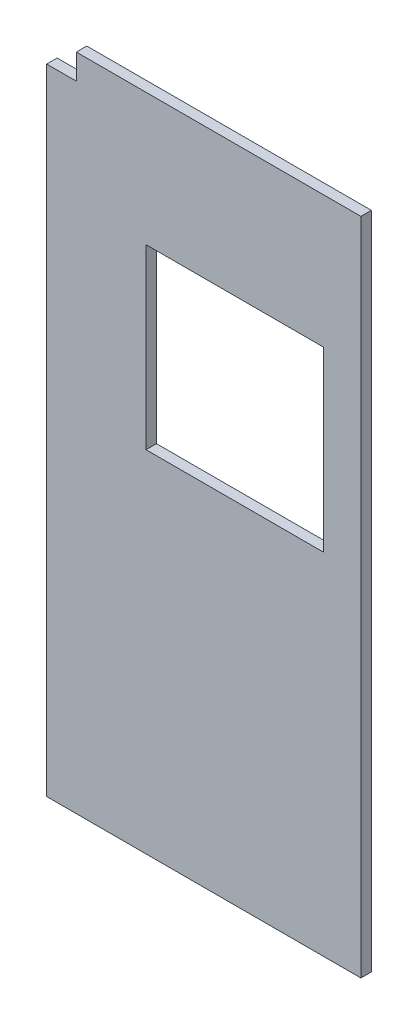
SolidWorks part; units mm, degrees
material "Polyurethane Foam Flexible"
ref_plane "Front Plane" through (0, 0, 0) normal (0, 0, 1) x (1, 0, 0)
ref_plane "Top Plane" through (0, 0, 0) normal (0, 1, 0) x (1, 0, 0)
ref_plane "Right Plane" through (0, 0, 0) normal (1, 0, 0) x (0, 0, -1)
sketch "Sketch1" plane through (0, 0, 0) normal (0, 0, 1) x (1, 0, 0)
  line L1 (-573.151, 1202.944) -> (573.151, 1202.944)
  line L2 (-573.151, 1202.944) -> (-573.151, -1202.944)
  line L3 (-573.151, -1202.944) -> (573.151, -1202.944)
  line L4 (573.151, 1202.944) -> (573.151, -1202.944)
  line L5 (-573.151, 1202.944) -> (573.151, -1202.944) construction
  line L6 (-573.151, -1202.944) -> (573.151, 1202.944) construction
  line L7 (-210.693, 721.614) -> (437.007, 721.614)
  line L8 (-210.693, 721.614) -> (-210.693, 73.914)
  line L9 (-210.693, 73.914) -> (437.007, 73.914)
  line L10 (437.007, 721.614) -> (437.007, 73.914)
  line L11 (-210.693, 721.614) -> (437.007, 73.914) construction
  line L12 (-210.693, 73.914) -> (437.007, 721.614) construction
  point P0 (0, 0)
  point P6 (113.157, 397.764)
  dimension "D1" = 1146.302
  dimension "D2" = 2405.888
  dimension "D3" = 1276.858
  dimension "D4" = 647.7
  dimension "D5" = 647.7
  dimension "D6" = 362.458
extrude "Boss-Extrude1" add sketch "Sketch1" along normal blind 38.1
sketch "Sketch2" plane through (0, 0, 38.1) normal (0, 0, 1) x (1, 0, 0)
  line L0 (573.151, 1202.944) -> (-573.151, 1202.944) construction
  line L1 (-573.151, 1202.944) -> (-464.947, 1202.944)
  line L2 (-573.151, 1202.944) -> (-573.151, 1110.996)
  line L3 (-573.151, 1110.996) -> (-464.947, 1110.996)
  line L4 (-464.947, 1202.944) -> (-464.947, 1110.996)
  line L5 (-573.151, 1202.944) -> (-464.947, 1110.996) construction
  line L6 (-573.151, 1110.996) -> (-464.947, 1202.944) construction
  line L7 (-573.151, 1202.944) -> (-573.151, -1202.944) construction
  point P0 (-519.049, 1156.97)
  dimension "D1" = 108.204
  dimension "D2" = 91.948
extrude "Cut-Extrude1" cut sketch "Sketch2" against normal up to surface (38.1 mm away) up to face at (0, 0, 0)
